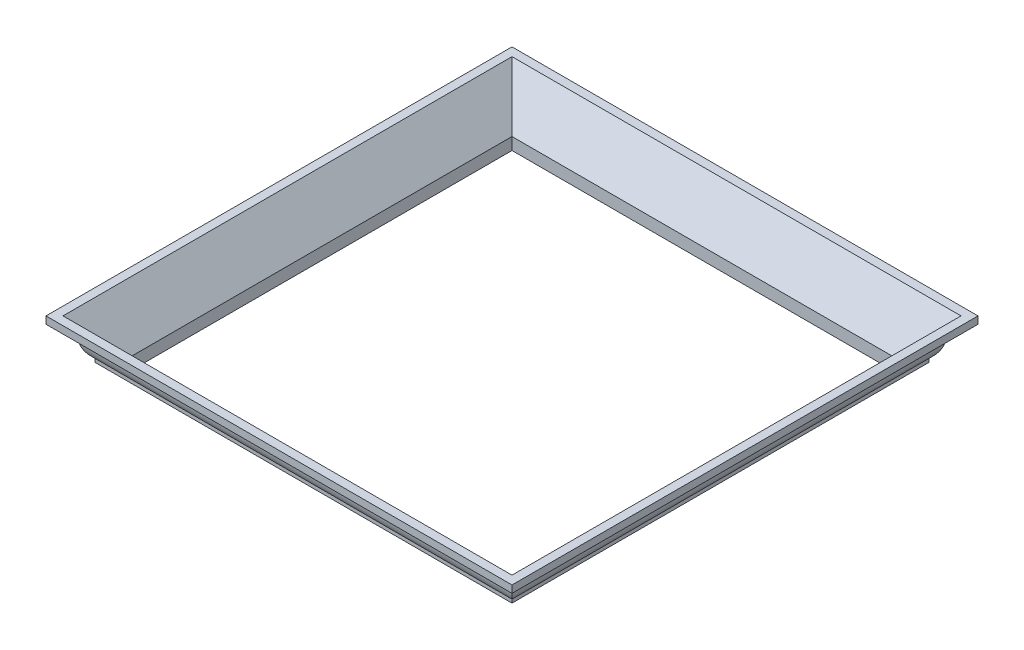
SolidWorks part; units mm, degrees
ref_plane "Front Plane" through (0, 0, 0) normal (0, 0, 1) x (1, 0, 0)
ref_plane "Top Plane" through (0, 0, 0) normal (0, 1, 0) x (1, 0, 0)
ref_plane "Right Plane" through (0, 0, 0) normal (1, 0, 0) x (0, 0, -1)
sketch "Sketch2" plane through (0, 0, 0) normal (0, 0, 1) x (1, 0, 0)
  line L0 (0, 0) -> (0, 31.75)
  line L1 (0, 31.75) -> (79.3786, 133.35)
  line L2 (79.3786, 133.35) -> (101.6, 133.35)
  line L3 (101.6, 133.35) -> (101.6, 114.3)
  line L4 (0, 0) -> (9.525, 0)
  line L5 (37.6153, 28.0903) -> (37.6153, 37.6153)
  line L6 (0, 31.75) -> (0, 93.8597) construction
  line L7 (102.2779, 69.85) -> (0, 93.8597) construction
  line L8 (0, 93.8597) -> (37.6153, 37.6153) construction
  arc A0 (9.525, 0) -> (37.6153, 28.0903) centre (37.6153, 0) cw
  arc A1 (37.6153, 37.6153) -> (58.9992, 80.0097) centre (1.6391, 82.352) ccw
  arc A2 (58.9992, 80.0097) -> (101.6, 114.3) centre (102.2779, 69.85) cw
  point P13 (58.9992, 80.0097)
  dimension "D1" = 101.6
  dimension "D2" = 133.35
  dimension "D3" = 9.525
  dimension "D4" = 9.525
  dimension "D5" = 19.05
  dimension "D6" = 44.45
  dimension "D7" = 31.75
  dimension "D8" = 38
extrude "Boss-Extrude1" add sketch "Sketch2" along normal blind 1219.2
sketch "Sketch3" plane through (0, 133.35, 0) normal (0, 1, 0) x (1, 0, 0)
  line L0 (101.6, 0) -> (0, 0)
  line L1 (0, 0) -> (0, -101.6)
  line L2 (0, -1219.2) -> (0, 0) construction
  line L3 (0, -101.6) -> (101.6, 0)
  line L4 (101.6, -1219.2) -> (0, -1219.2)
  line L5 (0, -1219.2) -> (0, -1117.6)
  line L6 (0, -1117.6) -> (101.6, -1219.2)
extrude "Cut-Extrude1" cut sketch "Sketch3" against normal through all
mirror "Mirror4" about plane through (0, 0, 1117.6) normal (0.7071, 0, -0.7071) of bodies 102
mirror "Mirror5" about plane through (-1016, 0, 1117.6) normal (0.7071, 0, 0.7071) of bodies 105
